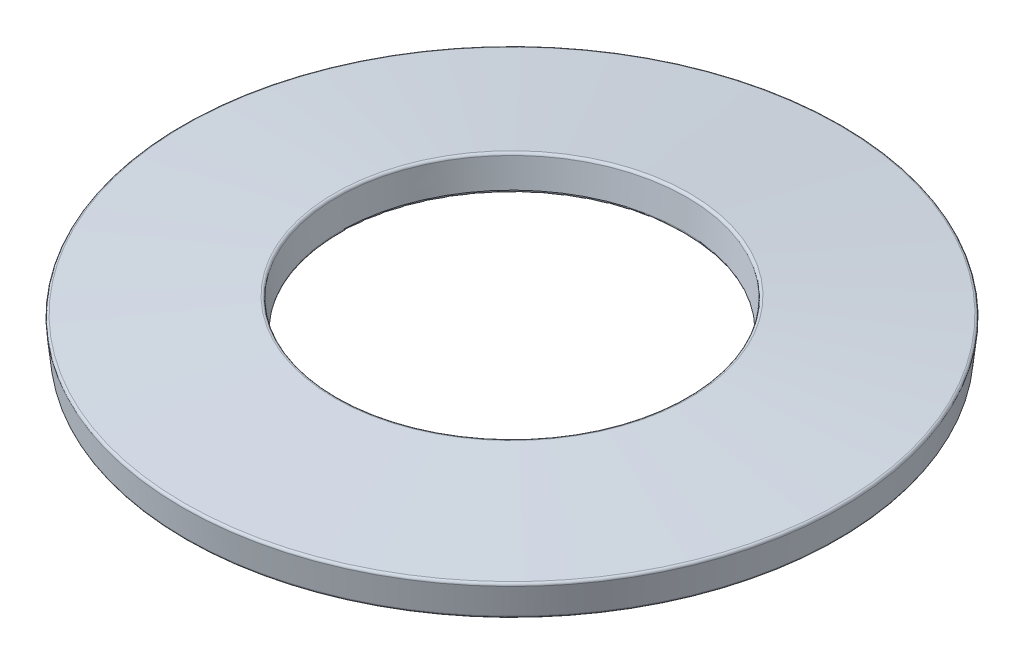
SolidWorks part; units mm, degrees
ref_plane "Front Plane" through (0, 0, 0) normal (0, 0, 1) x (1, 0, 0)
ref_plane "Top Plane" through (0, 0, 0) normal (0, 1, 0) x (1, 0, 0)
ref_plane "Right Plane" through (0, 0, 0) normal (1, 0, 0) x (0, 0, -1)
sketch "Sketch1" plane through (0, 0, 0) normal (0, 0, 1) x (1, 0, 0)
  line L0 (0, 0.375) -> (0, -0.375) construction
  line L1 (2.6536, 0.375) -> (5, 0.1221)
  line L2 (5, 0.1221) -> (4.9464, -0.375)
  line L3 (4.9464, -0.375) -> (2.6, -0.1221)
  line L4 (2.6, -0.1221) -> (2.6536, 0.375)
  line L5 (4.9464, -0.375) -> (2.5873, -0.3118) construction
  line L6 (2.5873, -0.3118) -> (2.6006, 0.188) construction
  line L7 (2.6006, 0.188) -> (4.9598, 0.1248) construction
  line L8 (4.9598, 0.1248) -> (4.9464, -0.375) construction
  line L9 (-4.9598, 0.1248) -> (-4.9464, -0.375) construction
  line L10 (-2.6006, 0.188) -> (-4.9598, 0.1248) construction
  line L11 (-2.5873, -0.3118) -> (-2.6006, 0.188) construction
  line L12 (-4.9464, -0.375) -> (-2.5873, -0.3118) construction
  point P11 (2.6006, 0.188)
  dimension "Thickness" = 0.5
  dimension "OD" = 10
  dimension "ID" = 5.2
  dimension "Height" = 0.75
  dimension "Compressed Height at Working Load" = 0.563
sketch "Sketch3" plane through (0, 0, 0) normal (0, 1, 0) x (1, 0, 0)
  circle A0 centre (0, 0) radius 2.6
  circle A1 centre (0, 0) radius 5
  dimension "D1" = 10
  dimension "D2" = 5.2
sketch "Sketch2" plane through (0, 0, 0) normal (0, 0, 1) x (1, 0, 0)
  line L4 (2.6, -0.1221) -> (2.6536, 0.375) construction
  line L5 (4.9464, -0.375) -> (2.6, -0.1221) construction
  line L6 (5, 0.1221) -> (4.9464, -0.375) construction
  line L7 (2.6536, 0.375) -> (5, 0.1221) construction
  line L8 (2.6, -0.1221) -> (2.6536, 0.375)
  line L9 (4.9464, -0.375) -> (2.6, -0.1221)
  line L10 (5, 0.1221) -> (4.9464, -0.375)
  line L11 (2.6536, 0.375) -> (5, 0.1221)
revolve "Revolve1" add sketch "Sketch2" angle 360 about L0
fillet "Fillet1" radius 0.0375 4 edges at (0, -0.1221, 2.6) (0, -0.375, 4.9464) (0, 0.1221, 5) (0, 0.375, 2.6536)
equation "\"D1@Fillet1\"=\"Thickness@Sketch1\"*0.075"
